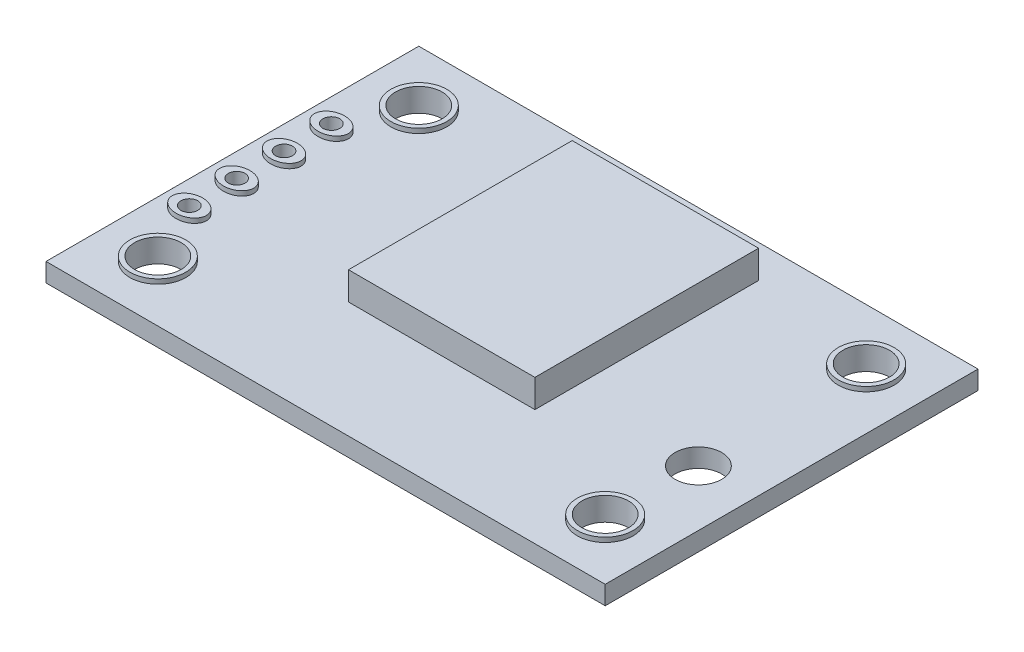
SolidWorks part; units mm, degrees
ref_plane "Front Plane" through (0, 0, 0) normal (0, 0, 1) x (1, 0, 0)
ref_plane "Top Plane" through (0, 0, 0) normal (0, 1, 0) x (1, 0, 0)
ref_plane "Right Plane" through (0, 0, 0) normal (1, 0, 0) x (0, 0, -1)
sketch "Sketch1" plane through (0, 0, 0) normal (0, 1, 0) x (1, 0, 0)
  line L0 (0, 17.792) -> (0, -17.792) construction
  line L1 (-15, 10) -> (15, 10)
  line L2 (-15, 10) -> (-15, -10)
  line L3 (-15, -10) -> (15, -10)
  line L4 (15, 10) -> (15, -10)
  line L5 (-25.3438, 0) -> (25.3438, 0) construction
  circle A0 centre (-12, 7) radius 1.25
  circle A1 centre (12, 7) radius 1.25
  circle A2 centre (12, -7) radius 1.25
  circle A3 centre (-12, -7) radius 1.25
  circle A4 centre (12, -2) radius 1.25
  point P0 (0, 0)
  point P8 (0, 10)
  point P13 (0, 0)
  point P15 (0, 0)
  dimension "D3" = 2.5
  dimension "D6" = 2.5
  dimension "D1" = 30
  dimension "D2" = 20
  dimension "D4" = 3
  dimension "D5" = 12
  dimension "D7" = 5
extrude "Boss-Extrude1" add sketch "Sketch1" along normal blind 1
sketch "Sketch2" plane through (0, 0, 0) normal (0, 1, 0) x (1, 0, 0)
  line L1 (-5, 8.2284) -> (5, 8.2284)
  line L2 (-5, 8.2284) -> (-5, -3.7716)
  line L3 (-5, -3.7716) -> (5, -3.7716)
  line L4 (5, 8.2284) -> (5, -3.7716)
  point P0 (0, 0)
  dimension "D1" = 10
  dimension "D2" = 12
extrude "Boss-Extrude2" add sketch "Sketch2" along normal blind 2.5
sketch "Sketch3" plane through (0, 1, 0) normal (0, 1, 0) x (1, 0, 0)
  line L0 (-15, 10) -> (-15, -10) construction
  line L1 (-6.6748, 0) -> (-17.3252, 0) construction
  circle A0 centre (-13.5, 3.81) radius 0.45
  circle A2 centre (-13.5, 1.27) radius 0.45
  circle A3 centre (-13.5, -1.27) radius 0.45
  circle A4 centre (-13.5, -3.81) radius 0.45
  circle A5 centre (-12, 7) radius 1.5
  circle A7 centre (12, 7) radius 1.5
  circle A8 centre (12, -7) radius 1.5
  circle A9 centre (-12, -7) radius 1.5
  circle A11 centre (-12, 7) radius 1.25
  circle A12 centre (12, 7) radius 1.25
  circle A13 centre (12, -7) radius 1.25
  circle A14 centre (-12, -7) radius 1.25
  ellipse E0 centre (-13.5, 3.81) end of major axis (-12.5832, 3.81) minor radius 0.7108
  ellipse E1 centre (-13.5, 1.27) end of major axis (-12.5832, 1.27) minor radius 0.7108
  ellipse E2 centre (-13.5, -1.27) end of major axis (-12.5832, -1.27) minor radius 0.7108
  ellipse E3 centre (-13.5, -3.81) end of major axis (-12.5832, -3.81) minor radius 0.7108
  point P8 (-12, 0)
  dimension "D1" = 0.9
  dimension "D5" = 3
  dimension "D6" = 3
  dimension "D7" = 3
  dimension "D2" = 1.5
  dimension "D3" = 1.27
  dimension "D4" = 2.54
extrude "Boss-Extrude3" add sketch "Sketch3" along normal blind 0.25
sketch "Sketch4" plane through (0, 0, 0) normal (0, 1, 0) x (1, 0, 0)
  circle A0 centre (-13.5, 3.81) radius 0.45
  circle A1 centre (-13.5, 1.27) radius 0.45
  circle A2 centre (-13.5, -1.27) radius 0.45
  circle A3 centre (-13.5, -3.81) radius 0.45
extrude "Cut-Extrude1" cut sketch "Sketch4" against normal blind 5 and the other way through all
